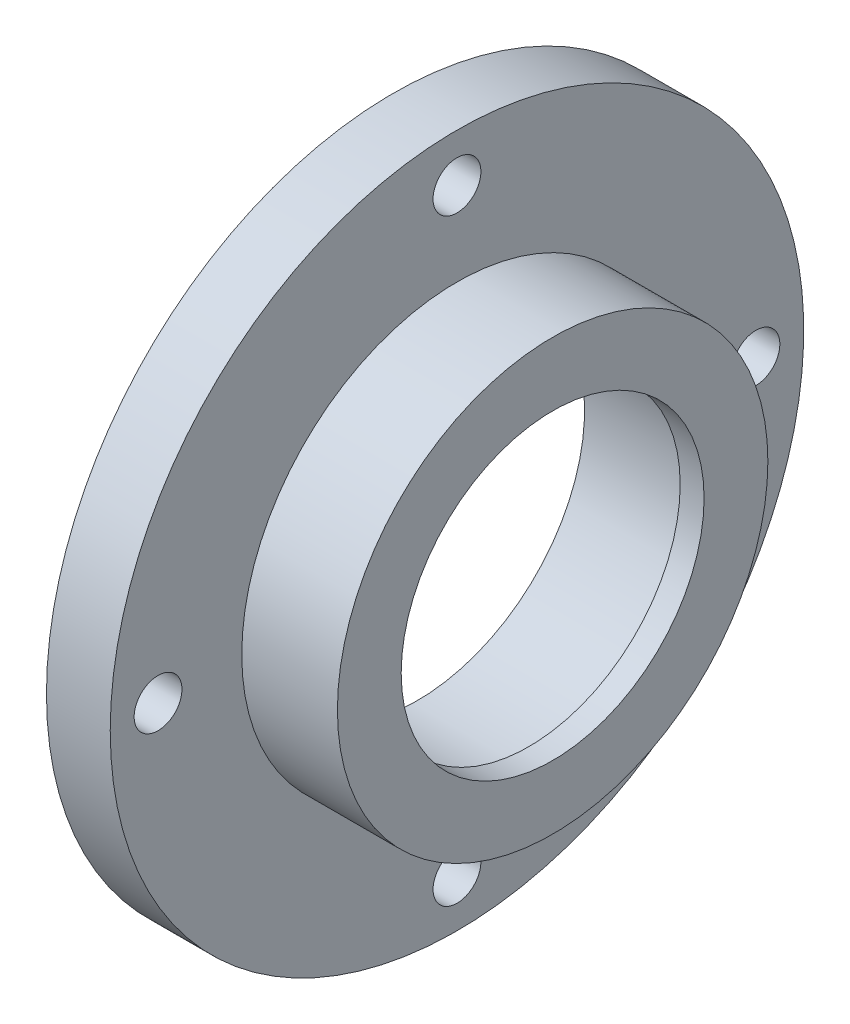
SolidWorks part; units mm, degrees
material "普通碳钢"
ref_plane "前视基准面" through (0, 0, 0) normal (0, 0, 1) x (1, 0, 0)
ref_plane "上视基准面" through (0, 0, 0) normal (0, 1, 0) x (1, 0, 0)
ref_plane "右视基准面" through (0, 0, 0) normal (1, 0, 0) x (0, 0, -1)
sketch "草图1" plane through (0, 0, 0) normal (0, 1, 0) x (1, 0, 0)
  line L0 (0, 0) -> (142.2397, 0) construction
  line L1 (0, 30) -> (0, 43.5)
  line L2 (0, 43.5) -> (8, 43.5)
  line L3 (8, 43.5) -> (8, 27)
  line L4 (8, 27) -> (20, 27)
  line L5 (0, 30) -> (3, 30)
  line L6 (3, 30) -> (3, 21)
  line L7 (20, 27) -> (20, 19)
  line L8 (20, 19) -> (17, 19)
  line L9 (17, 19) -> (17, 21)
  line L10 (17, 21) -> (3, 21)
  line L11 (0, 0) -> (0, 21) construction
  line L13 (0, 30) -> (0, 33.2156) construction
  point P17 (2.3498, 21.2155)
  dimension "D1" = 8
  dimension "D2" = 27
  dimension "D3" = 19
  dimension "D4" = 42
  dimension "D5" = 3
  dimension "D6" = 14
  dimension "D7" = 87
  dimension "D8" = 30
  dimension "D9" = 3
revolve "旋转1" add sketch "草图1" angle 360 about L0
sketch "草图2" plane through (0, 0, 0) normal (-1, 0, 0) x (0, 0, 1)
  line L0 (0, 0) -> (0, 37.5) construction
  circle A0 centre (0, 0) radius 37.5 construction
  circle A1 centre (0, 37.5) radius 3
  circle A2 centre (37.5, 0) radius 3
  circle A3 centre (0, -37.5) radius 3
  circle A4 centre (-37.5, 0) radius 3
  point P14 (0, 0)
  dimension "D1" = 6
  dimension "D3" = 75
  dimension "D2" = 4
extrude "切除-拉伸1" cut sketch "草图2" against normal up to next contours A3 | A1 | A4 | A2
equation "\"23。5\"=113.632"
